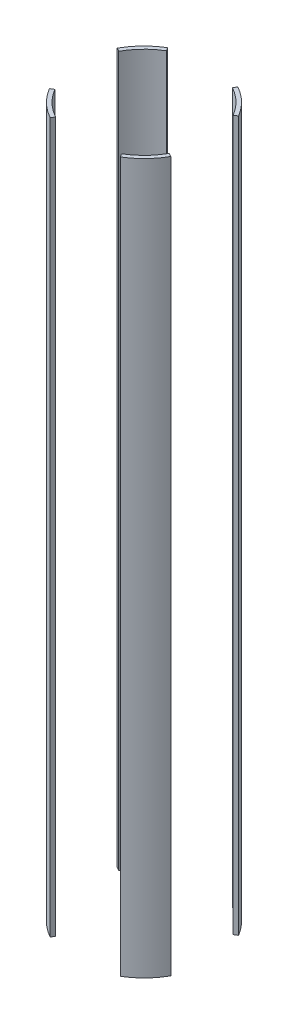
SolidWorks part; units mm, degrees
ref_plane "Front Plane" through (0, 0, 0) normal (0, 0, 1) x (1, 0, 0)
ref_plane "Top Plane" through (0, 0, 0) normal (0, 1, 0) x (1, 0, 0)
ref_plane "Right Plane" through (0, 0, 0) normal (1, 0, 0) x (0, 0, -1)
sketch "Sketch2" plane through (0, 0, 0) normal (0, 1, 0) x (1, 0, 0)
  circle A0 centre (0, 0) radius 88.9
  circle A1 centre (0, 0) radius 83.82
  dimension "D1" = 177.8
  dimension "D2" = 167.64
extrude "Boss-Extrude1" add sketch "Sketch2" along normal mid plane 914.4
sketch "Sketch3" plane through (0, 0, 0) normal (0, 1, 0) x (1, 0, 0)
  line L0 (0, 0) -> (169.6618, 101.6776)
  line L1 (-58.1167, 96.9749) -> (0, 0)
  line L2 (0, 0) -> (53.9, 96.9749)
  line L3 (53.9, 96.9749) -> (-58.1167, 96.9749)
  line L4 (0, 0) -> (70.9917, -118.4586)
  line L5 (70.9917, -118.4586) -> (-65.8409, -118.4586)
  line L6 (-65.8409, -118.4586) -> (0, 0)
  line L7 (169.6618, 101.6776) -> (169.6618, -94.3004)
  line L8 (169.6618, -94.3004) -> (0, 0)
  line L9 (0, 0) -> (-123.7413, 68.7771)
  line L10 (-123.7413, 68.7771) -> (-123.7413, -74.1577)
  line L11 (-123.7413, -74.1577) -> (0, 0)
  dimension "D1" = 60
  dimension "D2" = 60
  dimension "D3" = 60
  dimension "D4" = 60
  dimension "D5" = 30
  dimension "D6" = 30
extrude "Cut-Extrude1" cut sketch "Sketch3" against normal through all both and the other way through all contours L8 L7 L0 | L2 L3 L1 | L10 L11 L9 | L6 L5 L4
equation "\"D1@Boss-Extrude1\"=3*12"
